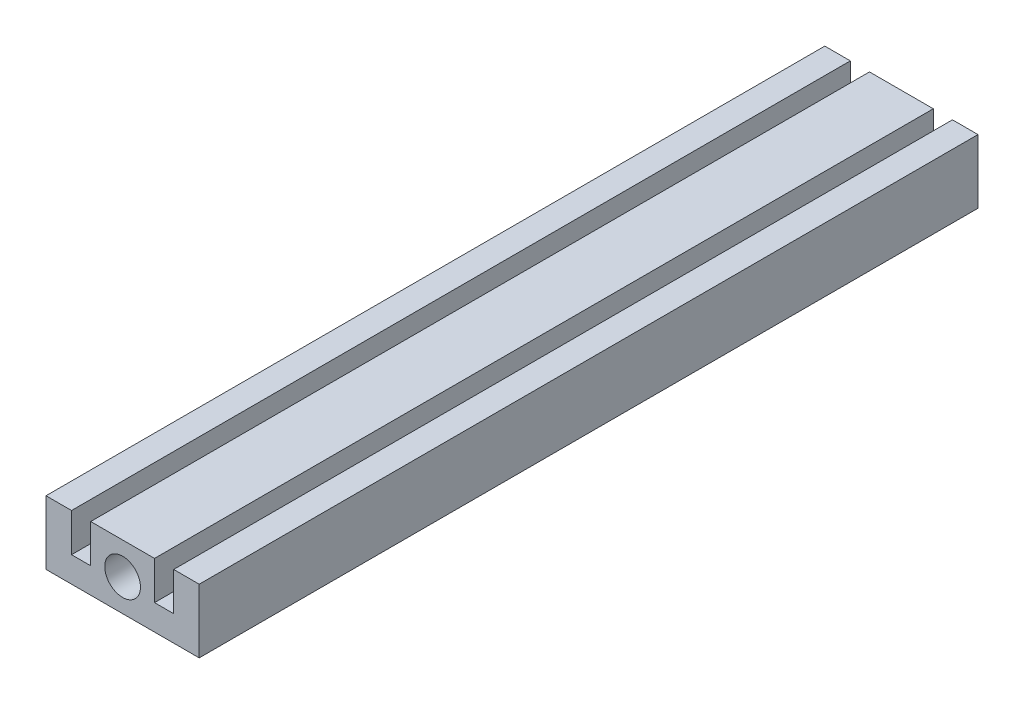
SolidWorks part; units mm, degrees
ref_plane "Plan de face" through (0, 0, 0) normal (0, 0, 1) x (1, 0, 0)
ref_plane "Plan de dessus" through (0, 0, 0) normal (0, 1, 0) x (1, 0, 0)
ref_plane "Plan de droite" through (0, 0, 0) normal (1, 0, 0) x (0, 0, -1)
sketch "Esquisse1" plane through (0, 0, 0) normal (0, 0, 1) x (1, 0, 0)
  line L0 (-12, 5) -> (-12, -5)
  line L1 (-12, -5) -> (12, -5)
  line L3 (5, 5) -> (-5, 5)
  line L4 (-5, 5) -> (-5, -1)
  line L5 (-5, -1) -> (-8, -1)
  line L6 (-8, -1) -> (-8, 5)
  line L7 (-8, 5) -> (-12, 5)
  line L8 (0, 5) -> (0, -5) construction
  line L9 (0, -55) -> (0, 55) construction
  line L10 (5, 5) -> (5, -1)
  line L11 (5, -1) -> (8, -1)
  line L12 (8, -1) -> (8, 5)
  line L13 (8, 5) -> (12, 5)
  line L14 (12, 5) -> (12, -5)
  circle A0 centre (0, 0) radius 2.8
  point P8 (-6.5, -1)
  point P9 (0, 5)
  point P14 (0, 0)
  dimension "D6" = 5.6
  dimension "D1" = 4
  dimension "D2" = 3
  dimension "D3" = 4
  dimension "D4" = 10
  dimension "D5" = 10
extrude "Boss.-Extru.1" add sketch "Esquisse1" along normal blind 122
